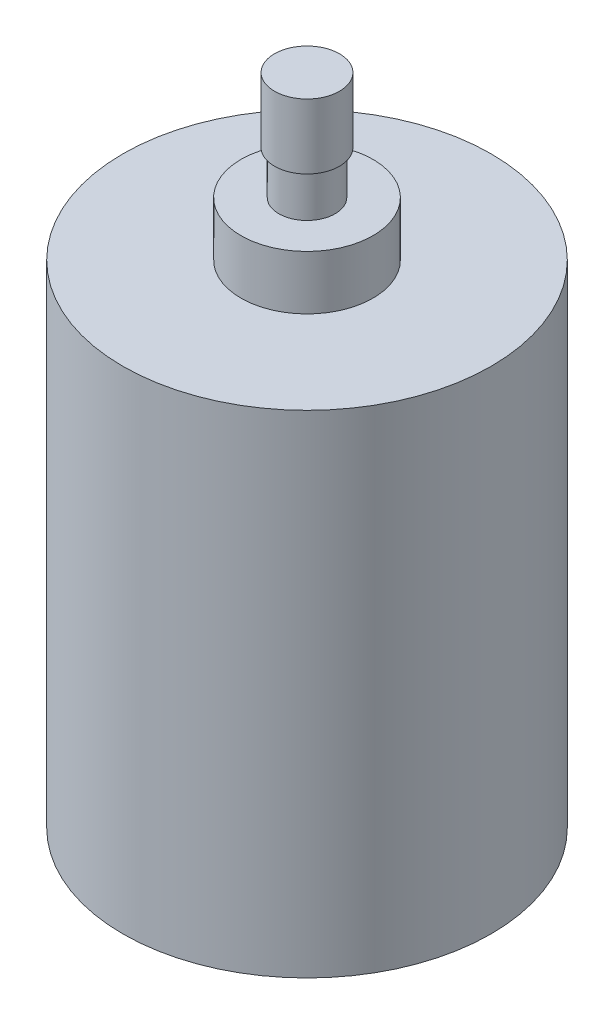
SolidWorks part; units mm, degrees
material "Custom Plastic"
ref_plane "Front Plane" through (0, 0, 0) normal (0, 0, 1) x (1, 0, 0)
ref_plane "Top Plane" through (0, 0, 0) normal (0, 1, 0) x (1, 0, 0)
ref_plane "Right Plane" through (0, 0, 0) normal (1, 0, 0) x (0, 0, -1)
sketch "Sketch2" plane through (0, 0, 0) normal (0, 0, 1) x (1, 0, 0)
  line L0 (-2.3, 0) -> (-8.5, 0)
  line L1 (-8.5, 0) -> (-8.5, 22.7)
  line L2 (-8.5, 22.7) -> (-3.05, 22.7)
  line L3 (-3.05, 22.7) -> (-3.05, 25.2)
  line L4 (-3.05, 25.2) -> (-1.3, 25.2)
  line L5 (-1.3, 25.2) -> (-1.3, 27.2)
  line L6 (-1.3, 27.2) -> (-1.5, 27.2)
  line L7 (-1.5, 27.2) -> (-1.5, 30.2)
  line L8 (-1.5, 30.2) -> (0, 30.2)
  line L9 (0, 30.2) -> (0, -2.5) construction
  line L10 (0, -2.5) -> (-2.3, -2.5)
  line L11 (-2.3, -2.5) -> (-2.3, 0)
  line L12 (0, 30.2) -> (0, -2.5)
  dimension "D1" = 8.5
  dimension "D2" = 3.05
  dimension "D3" = 22.7
  dimension "D4" = 2.3
  dimension "D5" = 2.5
  dimension "D6" = 1.3
  dimension "D7" = 1.5
  dimension "D8" = 2.5
  dimension "D9" = 2
  dimension "D10" = 3
revolve "Revolve1" add sketch "Sketch2" angle 360 about L9
